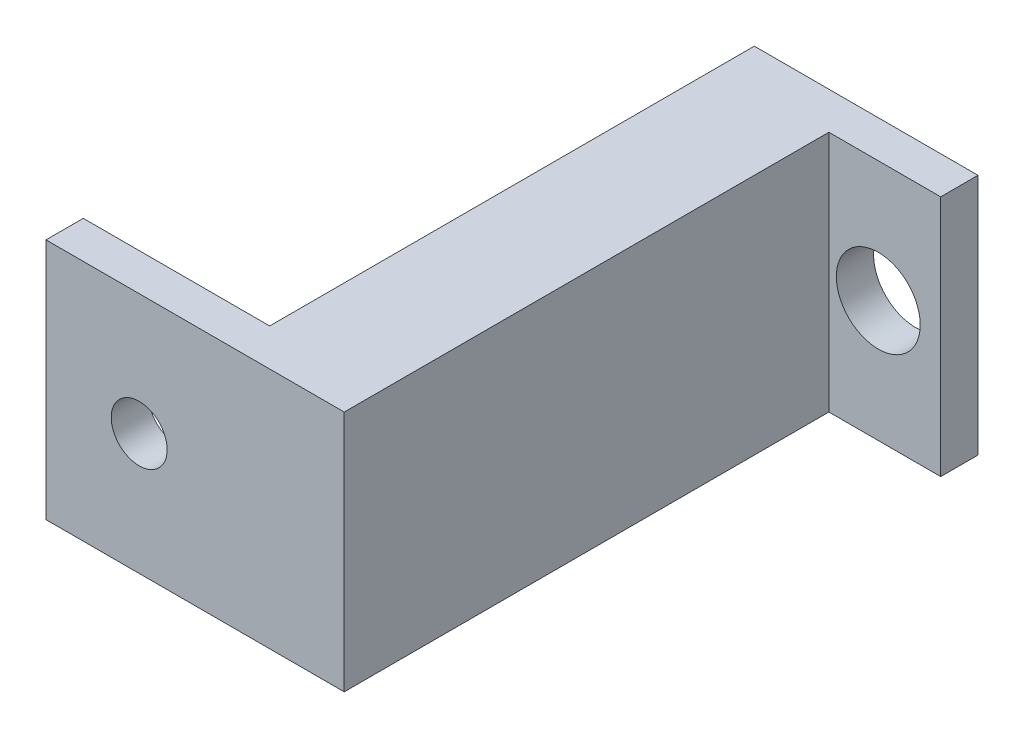
SolidWorks part; units mm, degrees
ref_plane "Płaszczyzna przednia" through (0, 0, 0) normal (0, 0, 1) x (1, 0, 0)
ref_plane "Płaszczyzna górna" through (0, 0, 0) normal (0, 1, 0) x (1, 0, 0)
ref_plane "Płaszczyzna prawa" through (0, 0, 0) normal (1, 0, 0) x (0, 0, -1)
sketch "Szkic1" plane through (0, 0, 0) normal (0, 0, 1) x (1, 0, 0)
  line L1 (-6, -6.5) -> (6, -6.5)
  line L2 (-6, -6.5) -> (-6, 6.5)
  line L3 (-6, 6.5) -> (6, 6.5)
  line L4 (6, -6.5) -> (6, 6.5)
  line L5 (-6, -6.5) -> (6, 6.5) construction
  line L6 (-6, 6.5) -> (6, -6.5) construction
  circle A0 centre (2.65, 0) radius 2.25
  point P0 (0, 0)
  dimension "D3" = 4.5
  dimension "D4" = 3.35
  dimension "D5" = 6.5
  dimension "D1" = 13
  dimension "D2" = 12
extrude "Dodanie-wyciągnięcie1" add sketch "Szkic1" along normal blind 2
sketch "Szkic2" plane through (0, 0, 2) normal (0, 0, 1) x (1, 0, 0)
  line L0 (-6, -6.5) -> (6, -6.5) construction
  line L1 (-6, 6.5) -> (0, 6.5)
  line L2 (-6, 6.5) -> (-6, -6.5)
  line L3 (-6, -6.5) -> (0, -6.5)
  line L4 (0, 6.5) -> (0, -6.5)
  dimension "D1" = 6
extrude "Dodanie-wyciągnięcie2" add sketch "Szkic2" along normal blind 24
sketch "Szkic3" plane through (0, 0, 26) normal (0, 0, 1) x (1, 0, 0)
  line L1 (0, 6.5) -> (-16, 6.5)
  line L2 (0, 6.5) -> (0, -6.5)
  line L3 (0, -6.5) -> (-16, -6.5)
  line L4 (-16, 6.5) -> (-16, -6.5)
  circle A0 centre (-11, 0) radius 1.5
  dimension "D2" = 3
  dimension "D3" = 5
  dimension "D4" = 6.5
  dimension "D1" = 16
extrude "Dodanie-wyciągnięcie3" add sketch "Szkic3" along normal blind 2
